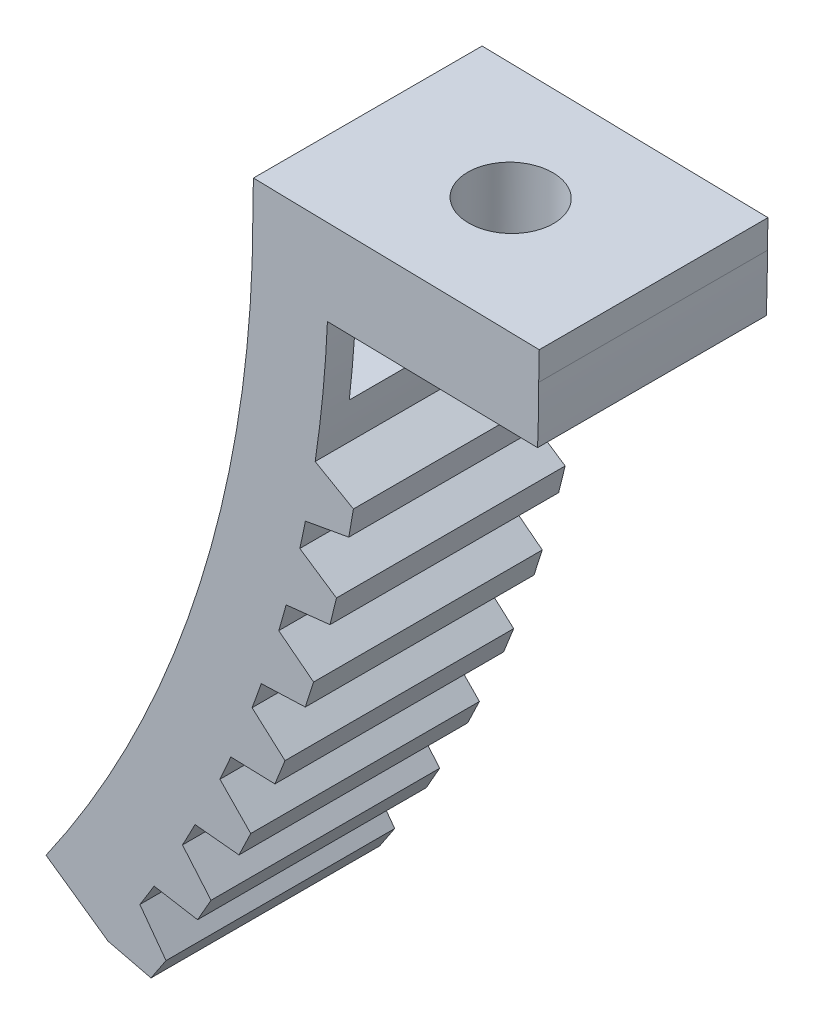
SolidWorks part; units mm, degrees
ref_plane "Front Plane" through (0, 0, 0) normal (0, 0, 1) x (1, 0, 0)
ref_plane "Top Plane" through (0, 0, 0) normal (0, 1, 0) x (1, 0, 0)
ref_plane "Right Plane" through (0, 0, 0) normal (1, 0, 0) x (0, 0, -1)
sketch "Sketch1" plane through (0, 0, 0) normal (0, 0, 1) x (1, 0, 0)
  line L0 (0, 0) -> (-10, 0)
  line L1 (-9.0424, -28.6788) -> (-17.2339, -22.9431)
  arc A0 (-9.0424, -28.6788) -> (0, 0) centre (-50, 0) ccw
  arc A1 (-17.2339, -22.9431) -> (-10, 0) centre (-50, 0) ccw
  dimension "D3" = 40
  dimension "D1" = 10
  dimension "D2" = 35
extrude "Extrude1" add sketch "Sketch1" along normal blind 8
sketch "Sketch3" plane through (0, 0, 0) normal (0, 0, 1) x (1, 0, 0)
  line L0 (-10, 0) -> (-10, 0.1999)
  line L1 (-10, 0.1999) -> (0, 0)
  line L2 (0, 0) -> (-10, 0)
  dimension "pedalangle" = 1.145
extrude "Extrude5" add sketch "Sketch3" along normal up to surface (8 mm away) up to face at (-8.0759, -13.2186, 8)
sketch "Sketch4" plane through (0, 0, 0) normal (0.02, 0.9998, 0) x (-0.9998, 0.02, 0)
  line L1 (10.002, 0) -> (0, 0)
  line L2 (10.002, 0) -> (10.002, 8)
  line L3 (10.002, 8) -> (0, 8)
  line L4 (0, 0) -> (0, 8)
extrude "Extrude6" add sketch "Sketch4" along normal blind 1
sketch "Sketch2" plane through (0.02, 0.9998, 0) normal (-0.02, -0.9998, 0) x (0.9998, -0.02, 0)
  line L0 (-10.002, 4) -> (0, 4) construction
  circle A0 centre (-5.001, 4) radius 1.5
  point P14 (-5.001, 4)
  dimension "D1" = 3
extrude "Extrude2" cut sketch "Sketch2" along normal blind 3
sketch "Sketch5" plane through (0, 0, 8) normal (0, 0, 1) x (1, 0, 0)
  line L0 (-0.04, -1.9996) -> (-7.3903, -1.8527)
  line L1 (-9.98, 1.1997) -> (0.02, 0.9998) construction
  line L2 (-15.0632, -24.463) -> (-9.0424, -28.6788)
  line L3 (-9.0424, -28.6788) -> (-2.9031, -26.1237)
  line L4 (-2.9031, -26.1237) -> (1.5975, -2.8502)
  line L5 (1.5975, -2.8502) -> (-0.04, -1.9996)
  line L6 (-17.2339, -22.9431) -> (-9.0424, -28.6788) construction
  arc A0 (-9.0424, -28.6788) -> (0, 0) centre (-50, 0) ccw construction
  arc A1 (-15.0632, -24.463) -> (-7.3903, -1.8527) centre (-50, 0) ccw
  arc A3 (-17.2339, -22.9431) -> (-10, 0) centre (-50, 0) ccw construction
  dimension "D1" = 85.3
  dimension "D2" = 3
extrude "Extrude7" cut sketch "Sketch5" against normal through all
sketch "Sketch6" plane through (-0.04, -1.9996, 0) normal (-0.02, -0.9998, 0) x (0.9998, -0.02, 0)
  line L0 (-7.3518, 0) -> (-7.3518, 8) construction
  line L1 (-7.3518, 7) -> (-11.6943, 7)
  line L2 (-7.3518, 7) -> (-7.3518, 1)
  line L3 (-7.3518, 1) -> (-11.6943, 1)
  line L4 (-11.6943, 7) -> (-11.6943, 1)
  line L5 (-5.001, 4) -> (-7.3518, 4) construction
  point P9 (-7.3518, 4)
  dimension "D1" = 6
extrude "Extrude8" cut sketch "Sketch6" along normal blind 3
sketch "Sketch7" plane through (0, 0, 8) normal (0, 0, 1) x (1, 0, 0)
  line L0 (-15.0632, -24.463) -> (-13.5637, -24.8273)
  line L1 (-13.5637, -24.8273) -> (-13.0373, -24.0365)
  line L2 (-13.0373, -24.0365) -> (-13.9518, -22.7936)
  line L3 (-13.9518, -22.7936) -> (-15.0632, -24.463)
  line L5 (-13.3005, -24.4319) -> (-37.3037, -8.4523) construction
  arc A0 (-15.0632, -24.463) -> (-7.3903, -1.8527) centre (-50, 0) ccw construction
  point P6 (0, 0)
  point P13 (-14.5075, -23.6283)
  dimension "D1" = 0.95
  dimension "D2" = 70
  dimension "D3" = 1.45
extrude "Extrude9" add sketch "Sketch7" against normal blind 8
pattern_circular "CirPattern1" count 7 over 23.8 about axis through (-50, 0, 0) along (0, 0, 1) of "Extrude9"
